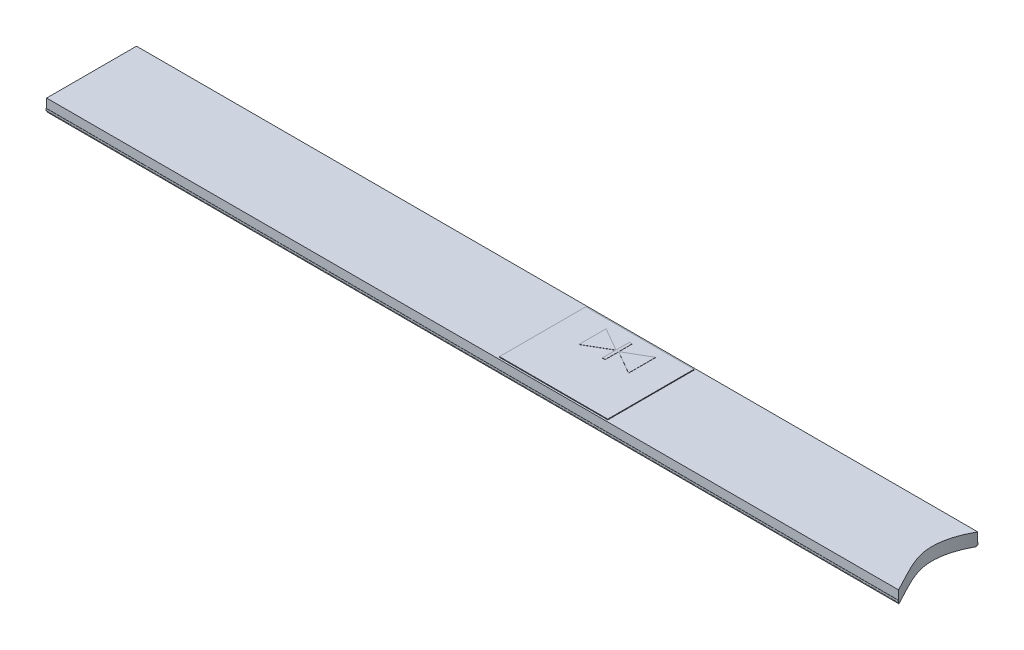
SolidWorks part; units mm, degrees
ref_plane "Front Plane" through (0, 0, 0) normal (0, 0, 1) x (1, 0, 0)
ref_plane "Top Plane" through (0, 0, 0) normal (0, 1, 0) x (1, 0, 0)
ref_plane "Right Plane" through (0, 0, 0) normal (1, 0, 0) x (0, 0, -1)
sketch "Sketch1" plane through (0, 0, 0) normal (1, 0, 0) x (0, 0, -1)
  line L0 (9.98, 0.3) -> (10, 0.3)
  line L2 (0, 0.1) -> (0, 0.3)
  line L3 (0, 0.3) -> (0.02, 0.3)
  line L4 (10, 0.1) -> (10, 0.3)
  line L6 (0.02, 0.3) -> (0.02, 1.3)
  line L7 (0.02, 1.3) -> (9.98, 1.3)
  line L8 (9.98, 0.3) -> (9.98, 1.3)
  line L10 (0.1, 0) -> (0.1, -0.1)
  line L11 (0.1, -0.1) -> (9.9, -0.1)
  line L12 (9.9, 0) -> (9.9, -0.1)
  arc A0 (0, 0.1) -> (0.1, 0) centre (0.1, 0.1) ccw
  arc A1 (10, 0.1) -> (9.9, 0) centre (9.9, 0.1) cw
  point P10 (0, 0)
  point P13 (10, 0)
  dimension "D6" = 0.1
  dimension "D1" = 9.96
  dimension "D2" = 0.02
  dimension "D3" = 10
  dimension "D7" = 0.1
  dimension "D8" = 0.1
extrude "Extrude1" add sketch "Sketch1" along normal blind 100
sketch "Sketch2" plane through (0, 0, 0) normal (1, 0, 0) x (0, 0, -1)
  line L1 (0.02, 0.3) -> (9.98, 0.3)
  line L2 (0.02, 0.3) -> (0.02, 1.3)
  line L3 (0.02, 1.3) -> (9.98, 1.3)
  line L4 (9.98, 0.3) -> (9.98, 1.3)
  line L5 (9.9, -0.1) -> (0.1, -0.1)
  line L6 (9.9, -0.1) -> (9.9, 0)
  line L7 (9.9, 0) -> (0.1, 0)
  line L8 (0.1, -0.1) -> (0.1, 0)
extrude "Extrude2" cut sketch "Sketch2" along normal blind 0.05
sketch "Sketch3" plane through (0, 1.3, 0) normal (0, 1, 0) x (1, 0, 0)
  spline S0 degree 3 poles (87.5505, 7.8218) (105.6161, 23.3493) (117.3854, 8.883) (109.7744, -0.1003) (120.9432, -13.4277) (86.8974, -25.6367) (98.8594, -3.7908) (87.5505, 7.8218) (105.6161, 23.3493) (117.3854, 8.883) knots -0.455467 -0.292152 -0.200977 0 0.128973 0.21007 0.316922 0.544533 0.707848 0.799023 1 1.128973 1.21007 1.316922 only from (106.9586, 17.1821) to (106.9586, 17.1821)
extrude "Extrude3" cut sketch "Sketch3" against normal blind 2
sketch "Sketch4" plane through (0, 1.3, 0) normal (0, 1, 0) x (1, 0, 0)
  line L0 (93.2974, 9.98) -> (0.05, 9.98) construction
  line L1 (50.05, 9.78) -> (62.05, 9.78)
  line L2 (50.05, 9.78) -> (50.05, 0.22)
  line L3 (50.05, 0.22) -> (62.05, 0.22)
  line L4 (62.05, 9.78) -> (62.05, 0.22)
  line L5 (94.4814, 0.02) -> (0.05, 0.02) construction
  line L6 (0.05, 9.98) -> (0.05, 0.02) construction
  dimension "D1" = 0.2
  dimension "D2" = 0.2
  dimension "D3" = 12
  dimension "D4" = 50
extrude "Extrude4" add sketch "Sketch4" along normal blind 0.08
sketch "Sketch5" plane through (0, 1.38, 0) normal (0, 1, 0) x (1, 0, 0)
  line L0 (56.05, 8.78) -> (56.05, 7.2312) construction
  line L1 (55.9, 7.2812) -> (53.304, 8.78)
  line L2 (53.304, 8.78) -> (53.304, 5.78)
  line L3 (53.304, 5.78) -> (55.9, 7.2788)
  line L4 (55.9, 8.78) -> (56.2, 8.78)
  line L5 (55.9, 8.78) -> (55.9, 7.2812)
  line L6 (55.9, 5.78) -> (56.2, 5.78)
  line L7 (56.2, 8.78) -> (56.2, 7.2812)
  line L8 (58.796, 5.78) -> (56.2, 7.2788)
  line L9 (56.2, 7.2812) -> (58.796, 8.78)
  line L10 (58.796, 8.78) -> (58.796, 5.78)
  line L11 (50.05, 9.78) -> (50.05, 0.22) construction
  line L12 (62.05, 9.78) -> (50.05, 9.78) construction
  line L13 (55.9, 7.2788) -> (55.9, 5.78)
  line L14 (56.2, 7.2788) -> (56.2, 5.78)
  circle A0 centre (54.17, 7.28) radius 0.866 construction
  circle A1 centre (57.93, 7.28) radius 0.866 construction
  dimension "D1" = 6
  dimension "D2" = 1
  dimension "D3" = 3
  dimension "D4" = 1.88
  dimension "D5" = 3
  dimension "D6" = 1.5
  dimension "D7" = 0.3
extrude "Extrude5" add sketch "Sketch5" along normal blind 0.02
